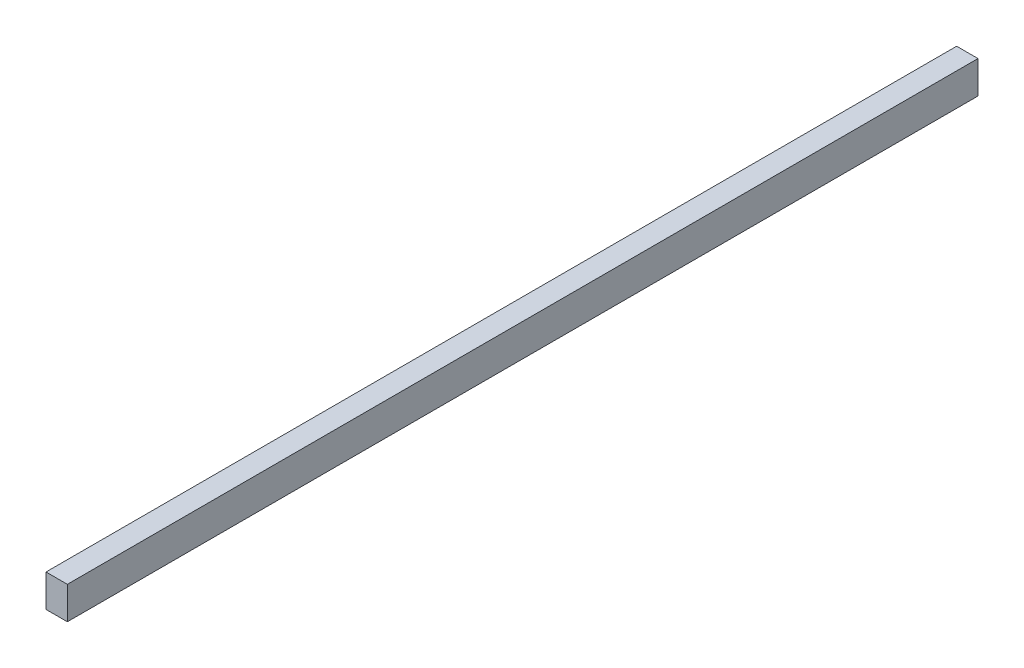
SolidWorks part; units mm, degrees
material "Pine"
ref_plane "Front Plane" through (0, 0, 0) normal (0, 0, 1) x (1, 0, 0)
ref_plane "Top Plane" through (0, 0, 0) normal (0, 1, 0) x (1, 0, 0)
ref_plane "Right Plane" through (0, 0, 0) normal (1, 0, 0) x (0, 0, -1)
sketch "Sketch1" plane through (0, 0, 0) normal (0, 0, 1) x (1, 0, 0)
  line L1 (-8.6951, 34.983) -> (29.4049, 34.983)
  line L2 (-8.6951, 34.983) -> (-8.6951, -22.9607)
  line L3 (-8.6951, -22.9607) -> (29.4049, -22.9607)
  line L4 (29.4049, 34.983) -> (29.4049, -22.9607)
  dimension "D1" = 38.1
  dimension "D2" = 57.9437
extrude "Boss-Extrude1" add sketch "Sketch1" along normal blind 1625.6
